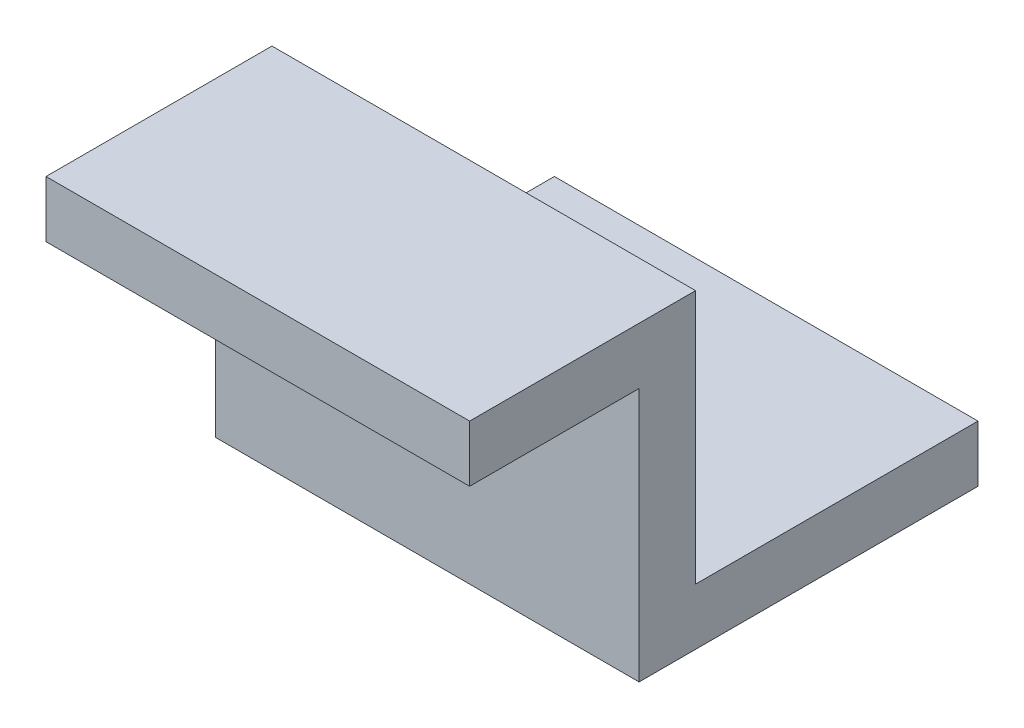
SolidWorks part; units mm, degrees
ref_plane "Front Plane" through (0, 0, 0) normal (0, 0, 1) x (1, 0, 0)
ref_plane "Top Plane" through (0, 0, 0) normal (0, 1, 0) x (1, 0, 0)
ref_plane "Right Plane" through (0, 0, 0) normal (1, 0, 0) x (0, 0, -1)
sketch "Sketch1" plane through (0, 0, 0) normal (1, 0, 0) x (0, 0, -1)
  line L0 (0, 0) -> (8, 0)
  line L1 (8, 0) -> (8, -9)
  line L2 (8, -9) -> (18, -9)
  line L3 (18, -9) -> (18, -11)
  line L4 (18, -11) -> (6, -11)
  line L5 (6, -11) -> (6, -2)
  line L6 (6, -2) -> (0, -2)
  line L7 (0, -2) -> (0, 0)
  dimension "D1" = 2
  dimension "D2" = 8
  dimension "D3" = 6
  dimension "D4" = 9
  dimension "D5" = 9
  dimension "D6" = 2
  dimension "D7" = 12
  dimension "D8" = 11
  dimension "D9" = 2
extrude "Boss-Extrude1" add sketch "Sketch1" against normal blind 15
sketch "Sketch3" plane through (0, -9, 0) normal (0, 1, 0) x (1, 0, 0)
  line L0 (-7.5, 18) -> (-7.5, 8) construction
  line L1 (-15, 18) -> (0, 18) construction
  line L2 (-15, 8) -> (0, 8) construction
  line L3 (0, 13) -> (-15, 13) construction
  line L4 (0, 18) -> (0, 8) construction
  line L5 (-15, 18) -> (-15, 8) construction
  circle A0 centre (-7.5, 13) radius 1.5
  dimension "D1" = 3
  dimension "D2" = 5
  dimension "D3" = 7.5
extrude "Cut-Extrude1" cut sketch "Sketch3" against normal up to next
